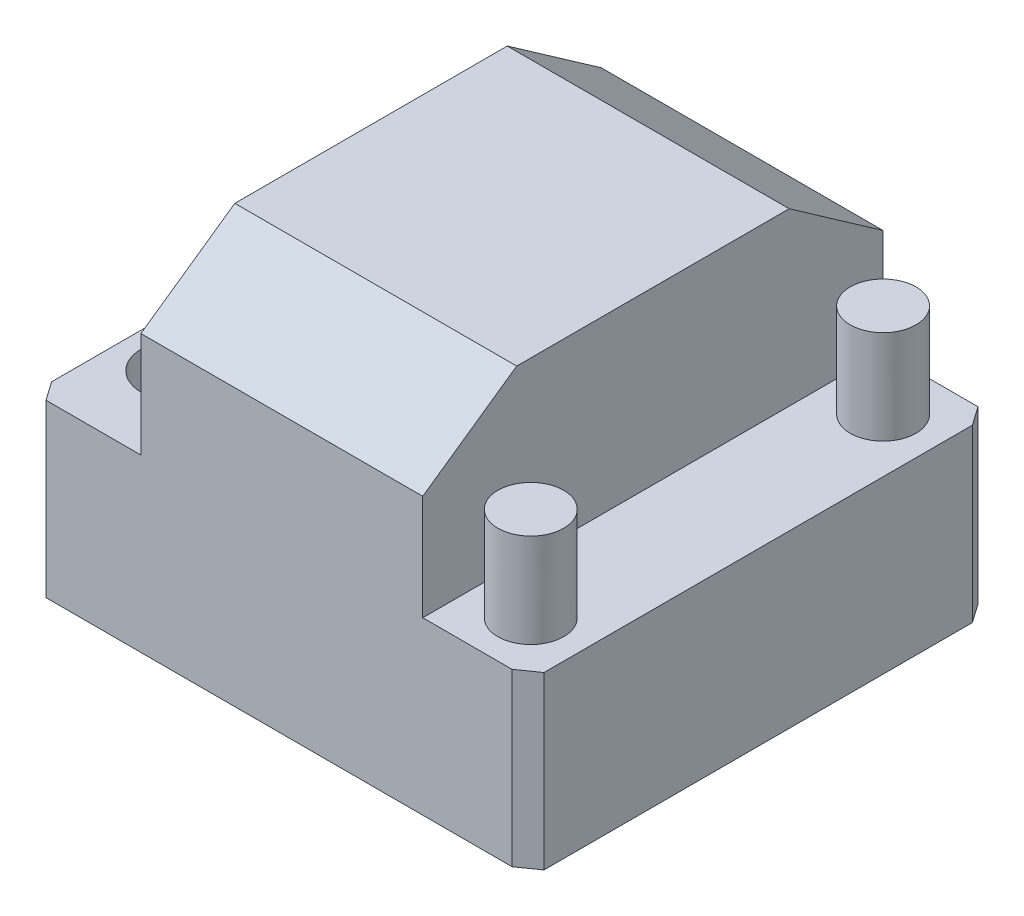
SolidWorks part; units mm, degrees
ref_plane "Front Plane" through (0, 0, 0) normal (0, 0, 1) x (1, 0, 0)
ref_plane "Top Plane" through (0, 0, 0) normal (0, 1, 0) x (1, 0, 0)
ref_plane "Right Plane" through (0, 0, 0) normal (1, 0, 0) x (0, 0, -1)
sketch "Sketch2" plane through (0, 0, 0) normal (0, 1, 0) x (1, 0, 0)
  line L0 (-26.5, -24.5) -> (26.5, 24.5) construction
  line L1 (-26.5, 24.5) -> (26.5, 24.5)
  line L2 (-26.5, 24.5) -> (-26.5, -24.5)
  line L3 (-26.5, -24.5) -> (26.5, -24.5)
  line L4 (26.5, 24.5) -> (26.5, -24.5)
  dimension "D1" = 53
  dimension "D2" = 49
extrude "Boss-Extrude1" add sketch "Sketch2" along normal blind 36.4
sketch "Sketch3" plane through (0, 0, 24.5) normal (0, 0, 1) x (1, 0, 0)
  line L0 (-26.5, 36.4) -> (-26.5, 0) construction
  line L1 (-26.5, 36.4) -> (-15, 36.4)
  line L2 (-26.5, 36.4) -> (-26.5, 18.2)
  line L3 (-26.5, 18.2) -> (-15, 18.2)
  line L4 (-15, 36.4) -> (-15, 18.2)
  line L6 (26.5, 36.4) -> (15, 36.4)
  line L7 (26.5, 36.4) -> (26.5, 18.2)
  line L8 (26.5, 18.2) -> (15, 18.2)
  line L9 (15, 36.4) -> (15, 18.2)
  dimension "D1" = 30
extrude "Cut-Extrude1" cut sketch "Sketch3" against normal through all
chamfer "Chamfer1" distance 10 angle 35 2 edges at (0, 36.4, -24.5) (0, 36.4, 24.5)
chamfer "Chamfer2" distance 2 angle 35 4 edges at (26.5, 9.1, -24.5) (26.5, 9.1, 24.5) (-26.5, 9.1, -24.5) (-26.5, 9.1, 24.5)
sketch "Sketch4" plane through (0, 18.2, 0) normal (0, 1, 0) x (1, 0, 0)
  line L0 (15, 24.5) -> (25.0996, 24.5) construction
  line L1 (26.5, 22.5) -> (26.5, -23.0996) construction
  line L2 (15, 14.5) -> (15, -14.5) construction
  line L3 (15, -24.5) -> (24.5, -24.5) construction
  circle A0 centre (20.75, -18.75) radius 5.75 construction
  circle A1 centre (20.75, 18.75) radius 5.75 construction
  circle A2 centre (20.75, -18.75) radius 3.5
  circle A3 centre (20.75, 18.75) radius 3.5
  dimension "D1" = 7
extrude "Boss-Extrude2" add sketch "Sketch4" along normal blind 10
sketch "Sketch5" plane through (0, 18.2, 0) normal (0, 1, 0) x (1, 0, 0)
  line L0 (-26.5, 0.2998) -> (-20.75, 0.2998) construction
  line L1 (-26.5, 23.0996) -> (-26.5, -22.5) construction
  line L2 (-20.75, 15.2998) -> (-20.75, -14.7002) construction
  line L3 (-15, 24.5) -> (-15, -24.5) construction
  circle A0 centre (-20.75, 0.2998) radius 5.75 construction
  circle A1 centre (-20.75, 15.2998) radius 4
  circle A2 centre (-20.75, -14.7002) radius 4
  circle A3 centre (-20.75, 0.2998) radius 4
  dimension "D2" = 8
  dimension "D1" = 30
extrude "Cut-Extrude2" cut sketch "Sketch5" against normal blind 10
